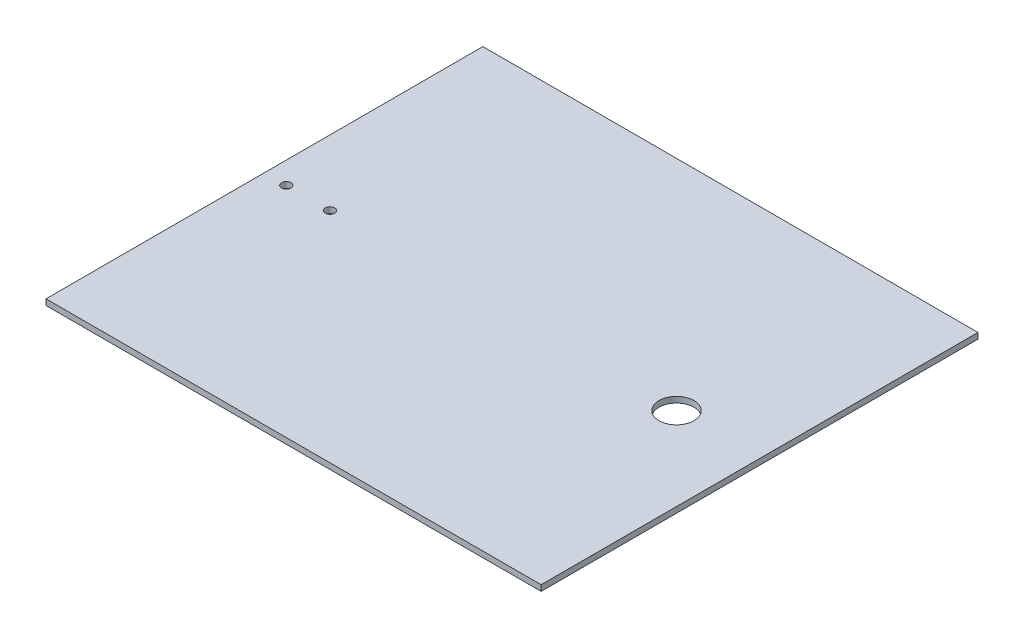
SolidWorks part; units mm, degrees
ref_plane "Front Plane" through (0, 0, 0) normal (0, 0, 1) x (1, 0, 0)
ref_plane "Top Plane" through (0, 0, 0) normal (0, 1, 0) x (1, 0, 0)
ref_plane "Right Plane" through (0, 0, 0) normal (1, 0, 0) x (0, 0, -1)
sketch "Sketch3" plane through (0, 0, 0) normal (0, 0, 1) x (1, 0, 0)
  line L0 (0, 0) -> (85, 0)
  line L1 (85, -2) -> (85, 0)
  line L3 (0, -2) -> (85, -2)
  line L7 (0, 0) -> (0, 38.371) construction
  line L11 (0, -2) -> (-85, -2)
  line L13 (-85, 0) -> (-85, -2)
  line L14 (0, 0) -> (-85, 0)
  line L15 (87.3174, 0) -> (84.9869, -20.2289) construction
  line L16 (85.0737, -2) -> (83, -20) construction
  line L17 (85, 0) -> (87.3174, 0) construction
  line L18 (85, -2) -> (85.0737, -2) construction
  point P0 (-84.8605, -2.267)
  dimension "D1" = 85
  dimension "D5" = 2
extrude "Boss-Extrude3" add sketch "Sketch3" along normal blind 150
sketch "Sketch4" plane through (0, 0, 0) normal (0, 1, 0) x (1, 0, 0)
  line L0 (-85, -150) -> (-85, 0) construction
  circle A0 centre (-77.5, -75) radius 1.6
  circle A1 centre (-62.5, -75) radius 1.6
  dimension "D3" = 3.2
  dimension "D4" = 3.2
  dimension "D1" = 15
  dimension "D2" = 7.5
extrude "Cut-Extrude1" cut sketch "Sketch4" against normal blind 10
sketch "Sketch5" plane through (0, 0, 0) normal (0, 1, 0) x (1, 0, 0)
  circle A0 centre (56.4852, -75) radius 6
  dimension "D1" = 12
extrude "Cut-Extrude2" cut sketch "Sketch5" against normal blind 10
